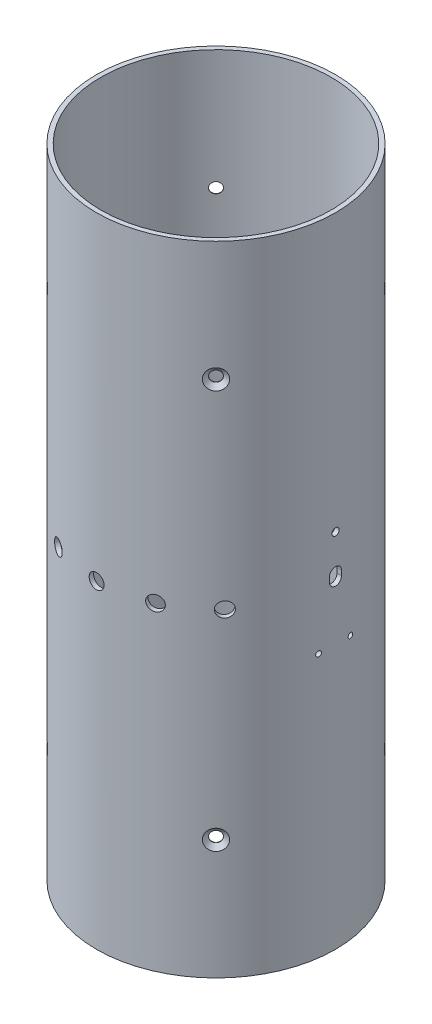
SolidWorks part; units mm, degrees
material "E-Glass Fiber"
ref_plane "Front Plane" through (0, 0, 0) normal (0, 0, 1) x (1, 0, 0)
ref_plane "Top Plane" through (0, 0, 0) normal (0, 1, 0) x (1, 0, 0)
ref_plane "Right Plane" through (0, 0, 0) normal (1, 0, 0) x (0, 0, -1)
sketch "Coupler Profile" plane through (0, 0, 0) normal (0, 1, 0) x (1, 0, 0)
  circle A0 centre (0, 0) radius 73.3425
  circle A1 centre (0, 0) radius 76.1746
  dimension "D1" = 146.685
  dimension "D2" = 152.3492
extrude "Coupler Body" add sketch "Coupler Profile" along normal blind 406.4
sketch "Sketch1" [suppressed] plane through (0, 0, 0) normal (0, 0, 1) x (1, 0, 0)
  line L0 (76.1746, 406.4) -> (-76.1746, 406.4) construction
  circle A0 centre (0, 76.2) radius 1.1906
  circle A1 centre (0, 330.2) radius 1.1906
  dimension "D3" = 2.3813
  dimension "D1" = 76.2
  dimension "D2" = 76.2
extrude "Cut-Extrude1" [suppressed] cut sketch "Sketch1" against normal through all both and the other way through all
ref_plane "Plane2" through (-53.8636, 0, 53.8636) normal (-0.7071, 0, 0.7071) x (0, -1, 0)
pattern_circular "CirPattern1" [suppressed] count 4 over 360
sketch "Center Axis" plane through (0, 0, 0) normal (0, 0, 1) x (1, 0, 0)
  line L0 (0, 0) -> (0, 406.4) construction
  line L1 (73.3425, 406.4) -> (-73.3425, 406.4) construction
ref_plane "Offset Plane" through (0, 0, 0) normal (0.866, 0, 0.5) x (0, 1, 0)
ref_plane "Plane1" through (0, 0, 76.1746) normal (0, 0, 1) x (1, 0, 0)
sketch "Sketch5" plane through (-53.8636, 0, 53.8636) normal (0.7071, 0, -0.7071) x (-0.7071, 0, -0.7071)
  line L0 (0, 406.4) -> (0, 0) construction
  line L1 (76.1746, 406.4) -> (-76.1746, 406.4) construction
  point P5 (0, 330.2)
  point P6 (0, 76.2)
  dimension "D1" = 76.2
  dimension "D2" = 76.2
hole_wizard "CSK for 1/4 Flat Head Machine Screw (100)1" positions "Sketch5" profile "Sketch7" countersink size "1/4" standard "ANSI Inch"
sketch "Sketch7" plane through (-53.8636, 76.2, 53.8636) normal (0, 1, 0) x (0.7071, 0, 0.7071)
  line L0 (0, 0) -> (0, 6.8558)
  line L1 (0, 6.8558) -> (3.3782, 4.826)
  line L2 (3.3782, 4.826) -> (3.3782, 2.5682)
  line L3 (3.3782, 2.5682) -> (6.4389, 0)
  line L5 (6.4389, 0) -> (0, 0)
  line L6 (-3.3782, 2.5682) -> (-6.4389, 0) construction
  line L10 (0, 6.8558) -> (-3.3782, 4.826) construction
  line L11 (0, -6.35) -> (0, 107.95) construction
  dimension "Hole Dia." = 6.7564
  dimension "Hole Depth" = 4.826
  dimension "Near C'Sink Dia." = 12.8778
  dimension "Near C'Sink Angle" = 100
  dimension "Drill Angle" = 118
pattern_circular "CirPattern2" count 4 every 90 about axis through (0, 406.4, 0) along (0, 1, 0) of "CSK for 1/4 Flat Head Machine Screw (100)1"
ref_plane "Plane3" through (0, 0, 76.1746) normal (0, 0, 1) x (1, 0, 0)
sketch "Sketch8" plane through (0, 0, 76.1746) normal (0, 0, 1) x (1, 0, 0)
  line L0 (0, 0) -> (0, 406.4) construction
  line L1 (76.1746, 406.4) -> (-76.1746, 406.4) construction
  point P5 (0, 203.2)
hole_wizard "3/8 (0.375) Diameter Hole1" positions "Sketch8" profile "Sketch9" hole size "3/8" standard "ANSI Inch"
sketch "Sketch9" plane through (0, 203.2, 76.1746) normal (1, 0, 0) x (0, -1, 0)
  line L0 (0, 0) -> (0, 2.8321)
  line L1 (0, 2.8321) -> (4.7625, 2.8321)
  line L2 (4.7625, 2.8321) -> (4.7625, 0)
  line L5 (4.7625, 0) -> (0, 0)
  line L11 (0, -6.35) -> (0, 107.95) construction
  dimension "Thru Hole Dia." = 9.525
  dimension "Thru Hole Depth" = 2.8321
pattern_circular "CirPattern3" count 3 every 24 about axis through (0, 406.4, 0) along (0, 1, 0) of "3/8 (0.375) Diameter Hole1"
ref_plane "Plane4" through (76.1746, 0, 0) normal (1, 0, 0) x (0, 0, -1)
sketch "Sketch10" plane through (76.1746, 0, 0) normal (1, 0, 0) x (0, 0, -1)
  line L0 (0, 0) -> (0, 406.4) construction
  line L1 (76.1746, 406.4) -> (-76.1746, 406.4) construction
  line L3 (-16.24, 243.8193) -> (16.24, 243.8193) construction
  line L4 (-16.24, 243.8193) -> (-16.24, 162.5807) construction
  line L5 (-16.24, 162.5807) -> (16.24, 162.5807) construction
  line L6 (16.24, 243.8193) -> (16.24, 162.5807) construction
  circle A0 centre (-10.1395, 167.768) radius 1.651
  circle A1 centre (10.1395, 167.768) radius 1.651
  circle A2 centre (0, 230.3499) radius 2.286
  point P15 (0, 0)
  dimension "D4" = 3.302
  dimension "D5" = 4.572
  dimension "D1" = 10.1395
  dimension "D2" = 10.1395
  dimension "D3" = 62.5819
  dimension "D6" = 6.1005
  dimension "D7" = 6.1005
  dimension "D8" = 5.1873
  dimension "D9" = 13.4694
  dimension "D10" = 162.5807
extrude "Cut-Extrude2" cut sketch "Sketch10" against normal up to next
sketch "Sketch11" plane through (76.1746, 0, 0) normal (1, 0, 0) x (0, 0, -1)
  line L0 (0, 0) -> (0, 406.4) construction
  line L1 (76.1746, 406.4) -> (-76.1746, 406.4) construction
  line L2 (-3.81, 207.3376) -> (-3.81, 204.234)
  line L3 (3.81, 207.3376) -> (3.81, 204.234)
  line L4 (-10.1395, 167.768) -> (10.1395, 167.768) construction
  arc A0 (3.81, 207.3376) -> (-3.81, 207.3376) centre (0, 207.3376) ccw
  arc A1 (-3.81, 204.234) -> (3.81, 204.234) centre (0, 204.234) ccw
  arc A2 (0, 208.044) -> (-3.4797, 205.7858) centre (0, 204.234) ccw construction
  arc A3 (-3.4797, 205.7858) -> (0, 203.5276) centre (0, 207.3376) ccw construction
  arc A4 (3.4797, 205.7858) -> (0, 208.044) centre (0, 204.234) ccw construction
  arc A5 (0, 203.5276) -> (3.4797, 205.7858) centre (0, 207.3376) ccw construction
  arc A6 (3.81, 204.234) -> (3.4797, 205.7858) centre (0, 204.234) ccw construction
  arc A7 (3.4797, 205.7858) -> (3.81, 207.3376) centre (0, 207.3376) ccw construction
  arc A8 (-3.81, 207.3376) -> (-3.4797, 205.7858) centre (0, 207.3376) ccw construction
  arc A9 (-3.4797, 205.7858) -> (-3.81, 204.234) centre (0, 204.234) ccw construction
  dimension "D1" = 7.62
  dimension "D2" = 3.1036
  dimension "D3" = 36.466
extrude "Cut-Extrude4" cut sketch "Sketch11" against normal up to next
equation "\"Length\"=16"
equation "\"Outer Diameter\"= 5.998"
equation "\"Inner Diameter\"= 5.775"
equation "\"Wall Thickness\"= 0.111"
equation "\"D1@Coupler Profile\" = \"Inner Diameter\""
equation "\"D2@Coupler Profile\" = \"Outer Diameter\""
equation "\"D1@Coupler Body\" = \"Length\""
equation "\"Shear Pin Dia\"= 3 / 32"
equation "\"Shear Pin Offset\"= 3"
equation "\"D1@Sketch1\"=\"Shear Pin Offset\""
equation "\"D2@Sketch1\"=\"Shear Pin Offset\""
equation "\"D3@Sketch1\"=\"Shear Pin Dia\""
equation "\"Key Hole Dia\"=0.375"
equation "\"D1@Sketch5\"=\"Shear Pin Offset\""
equation "\"D2@Sketch5\"=\"Shear Pin Offset\""
equation "\"D10@Sketch10\"=(16-3.19837298)/2"
